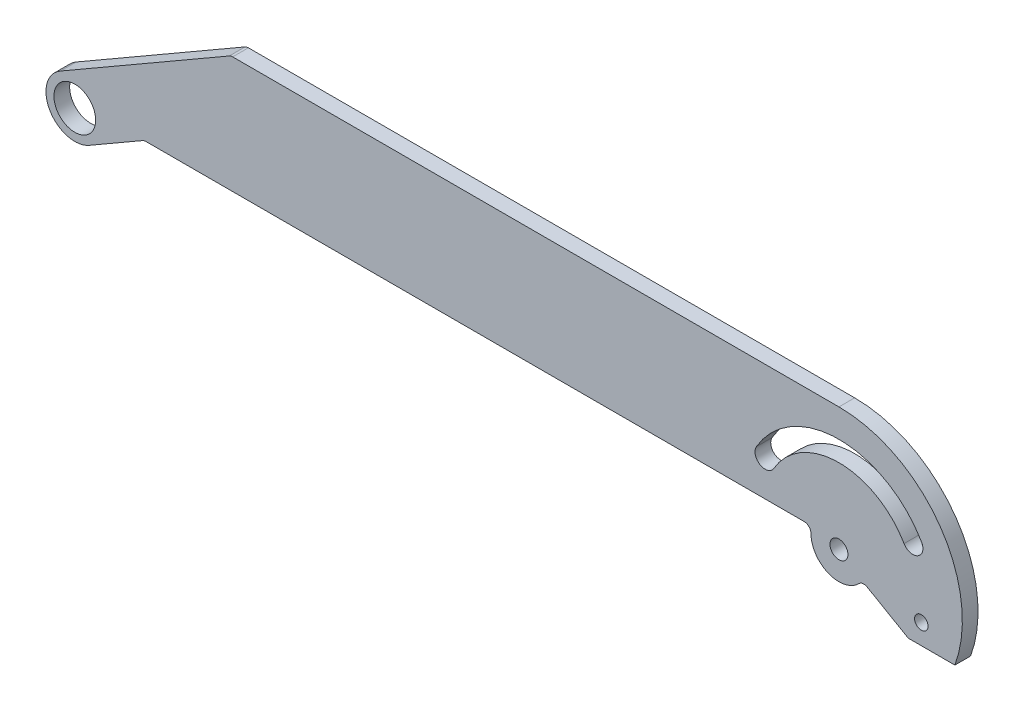
SolidWorks part; units mm, degrees
ref_plane "Front Plane" through (0, 0, 0) normal (0, 0, 1) x (1, 0, 0)
ref_plane "Top Plane" through (0, 0, 0) normal (0, 1, 0) x (1, 0, 0)
ref_plane "Right Plane" through (0, 0, 0) normal (1, 0, 0) x (0, 0, -1)
sketch "Sketch1" plane through (0, 0, 0) normal (0, 0, 1) x (1, 0, 0)
  line L0 (0, 0) -> (340.6, 0) construction
  line L1 (340.6, 0) -> (373.509, 19) construction
  line L2 (340.6, 0) -> (307.691, 19) construction
  line L3 (340.6, 0) -> (377.3052, -9.8351) construction
  line L5 (-50, -75) -> (450, -75)
  line L6 (-50, -75) -> (-50, 75)
  line L7 (-50, 75) -> (450, 75)
  line L8 (450, -75) -> (450, 75)
  circle A0 centre (0, 0) radius 9.3
  circle A1 centre (340.6, 0) radius 4
  circle A2 centre (373.509, 19) radius 4.5
  circle A3 centre (307.691, 19) radius 4.5
  circle A4 centre (377.3052, -9.8351) radius 3
  circle A5 centre (340.6, 0) radius 42.5
  circle A6 centre (340.6, 0) radius 33.5
  dimension "D1" = 340.6
  dimension "D2" = 38
  dimension "D6" = 8
  dimension "D7" = 6
  dimension "D8" = 9
  dimension "D9" = 9
  dimension "D12" = 18.6
  dimension "D3" = 165
  dimension "D4" = 150
  dimension "D5" = 120
  dimension "D10" = 38
  dimension "D11" = 38
  dimension "D13" = 150
  dimension "D14" = 500
  dimension "D15" = 75
  dimension "D16" = 50
extrude "Boss-Extrude1" add sketch "Sketch1" along normal blind 7 contours L5 L8 L7 L6 A5 A0 | A6 A3 A5 A2 A4 | A6 A1
sketch "Sketch3" plane through (0, 0, 7) normal (0, 0, 1) x (1, 0, 0)
  line L0 (-50, 55) -> (450, 55)
  line L1 (340.6, 0) -> (350.9687, -6.9813) construction
  line L2 (-50, -75) -> (-50, 75) construction
  line L3 (450, -75) -> (450, 75) construction
  line L4 (-6.425, 11.1284) -> (69.5628, 55)
  line L5 (0, 0) -> (-6.425, 11.1284) construction
  line L6 (0, 0) -> (6.425, -11.1284) construction
  line L7 (-50, 3) -> (450, 3) construction
  line L8 (6.425, -11.1284) -> (30.8962, 3)
  line L9 (30.8962, 3) -> (328.4653, 3)
  line L10 (450, -18.8351) -> (-50, -18.8351) construction
  line L11 (350.9687, -6.9813) -> (371.4981, -18.8351)
  line L12 (371.4981, -18.8351) -> (392.2743, -18.8351)
  circle A0 centre (0, 0) radius 12.85
  circle A1 centre (377.3052, -9.8351) radius 3 construction
  circle A2 centre (340.6, 0) radius 12.5
  circle A3 centre (340.6, 0) radius 55
  line M7 (-50, -75) -> (450, -75)
  line M8 (450, -75) -> (450, 75)
  line M9 (450, 75) -> (-50, 75)
  line M10 (-50, 75) -> (-50, -75)
  dimension "D1" = 25.7
  dimension "D4" = 9
  dimension "D5" = 25
  dimension "D2" = 55
  dimension "D3" = 3
  dimension "D6" = 23.7059
  dimension "D7" = 149.998
  dimension "D8" = 30
  dimension "D9" = 150
  dimension "D10" = 28.2569
extrude "Cut-Extrude1" cut sketch "Sketch3" against normal blind 7 contours A3 L9 L8 A0 L4 L0 M10 M7 M8 | L9 A3 L12 L11 A2 | L0 M10 M8 M9
fillet "Fillet2" radius 3 4 edges at (69.5628, 55, 3.5) (30.8962, 3, 3.5) (350.9687, -6.9813, 3.5) (328.4653, 3, 3.5)
